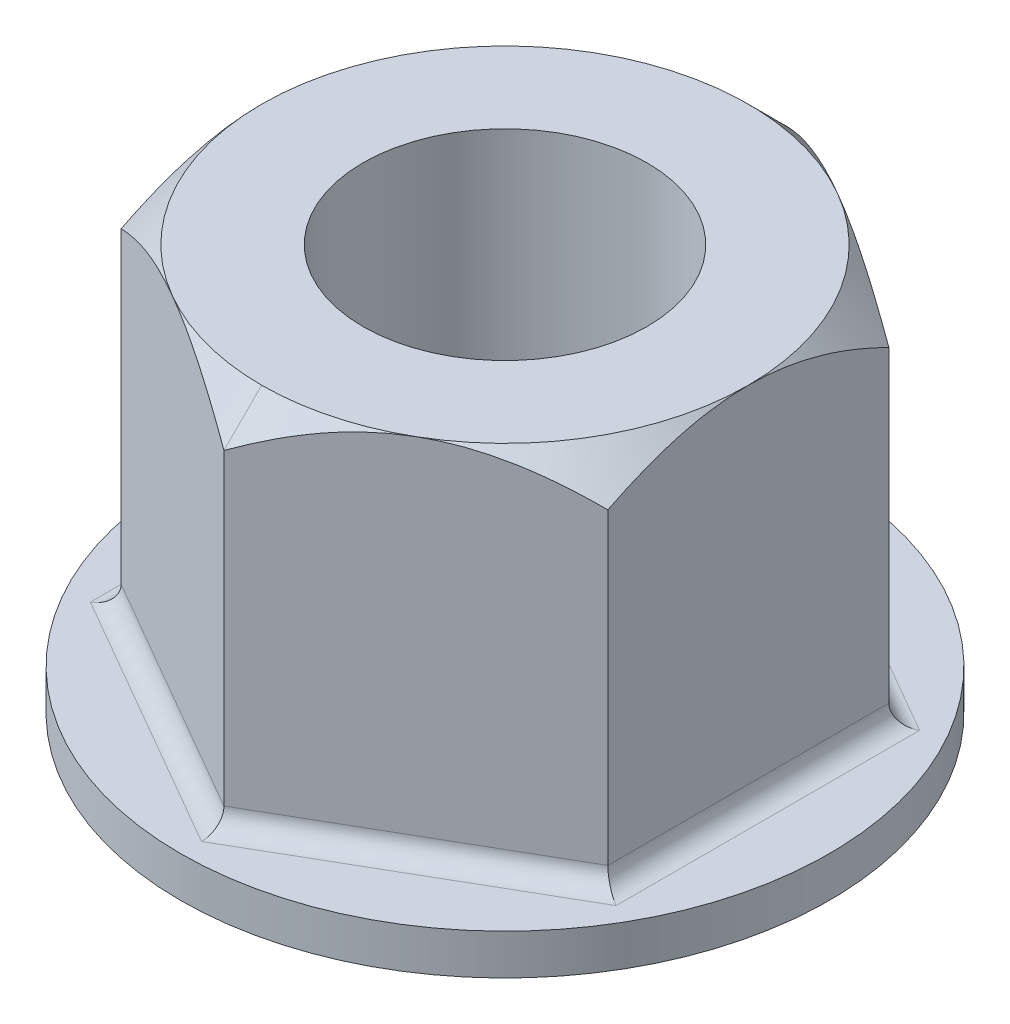
SolidWorks part; units mm, degrees
ref_plane "Front Plane" through (0, 0, 0) normal (0, 0, 1) x (1, 0, 0)
ref_plane "Top Plane" through (0, 0, 0) normal (0, 1, 0) x (1, 0, 0)
ref_plane "Right Plane" through (0, 0, 0) normal (1, 0, 0) x (0, 0, -1)
sketch "Sketch2" plane through (0, 0, 0) normal (0, 1, 0) x (1, 0, 0)
  circle A0 centre (0, 0) radius 25.4
  dimension "D1" = 50.8
extrude "Boss-Extrude1" add sketch "Sketch2" along normal blind 3.175
sketch "Sketch3" plane through (0, 3.175, 0) normal (0, 1, 0) x (1, 0, 0)
  line L1 (0, 21.997) -> (-19.05, 10.9985)
  line L2 (-19.05, 10.9985) -> (-19.05, -10.9985)
  line L3 (-19.05, -10.9985) -> (0, -21.997)
  line L4 (0, -21.997) -> (19.05, -10.9985)
  line L5 (19.05, -10.9985) -> (19.05, 10.9985)
  line L6 (19.05, 10.9985) -> (0, 21.997)
  circle A0 centre (0, 0) radius 19.05 construction
  point P1 (0, 0)
  dimension "D1" = 38.1
extrude "Boss-Extrude2" add sketch "Sketch3" along normal blind 28.575
hole_wizard "1-8 Tapped Hole1" positions "Sketch4" profile "Sketch5" tap size "1-8" standard "ANSI Inch" end condition up to next
sketch "Sketch4" plane through (0, 31.75, 0) normal (0, 1, 0) x (1, 0, 0)
  point P0 (0, 0)
sketch "Sketch5" plane through (0, 31.75, 0) normal (1, 0, 0) x (0, 0, 1)
  line L0 (0, 0) -> (0, 31.75)
  line L1 (0, 31.75) -> (11.1125, 31.75)
  line L2 (11.1125, 31.75) -> (11.1125, 0)
  line L5 (11.1125, 0) -> (0, 0)
  line L11 (0, -6.35) -> (0, 107.95) construction
  dimension "Thru Tap Drill Dia." = 22.225
  dimension "Thru Tap Drill Depth" = 31.75
cosmetic thread "Hole Thread1" parameters "D2"=25.4
sketch "Sketch7" plane through (0, 31.75, 0) normal (0, 1, 0) x (1, 0, 0)
  circle A1 centre (0, 0) radius 19.05
sketch "Sketch8" plane through (0, 0, 0) normal (1, 0, 0) x (0, 0, -1)
  line L1 (-21.997, 31.75) -> (-21.997, 3.175) construction
  line L5 (-21.997, 28.803) -> (-21.997, 31.75)
  line L9 (-21.997, 28.803) -> (-19.05, 31.75)
  line L10 (-19.05, 31.75) -> (-21.997, 31.75)
  point P0 (0, 0)
  dimension "D1" = 45
sweep "Cut-Sweep1" cut profiles "Sketch8" path "Sketch7"
fillet "Fillet1" radius 1.524 6 edges at (9.525, 3.175, -16.4978) (-9.525, 3.175, -16.4978) (-19.05, 3.175, 0) (-9.525, 3.175, 16.4978) (19.05, 3.175, 0) (9.525, 3.175, 16.4978)
